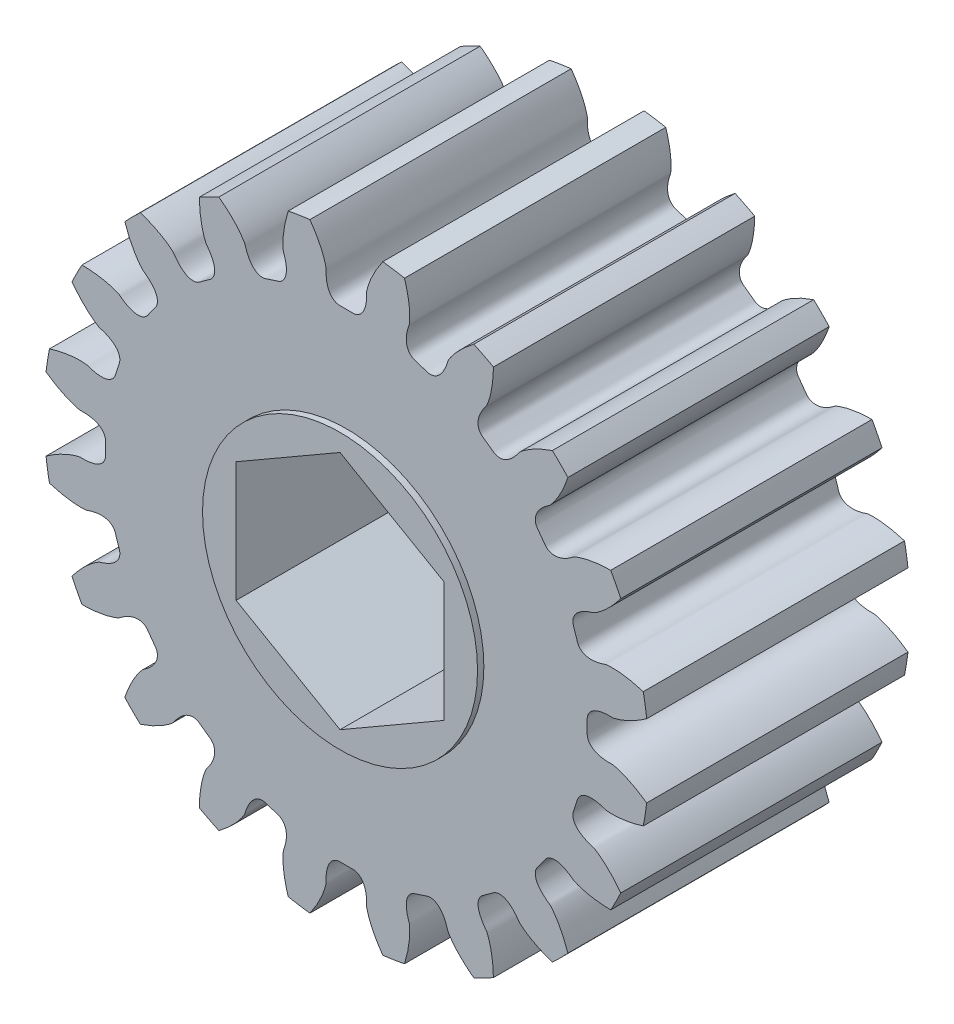
SolidWorks part; units mm, degrees
material "7075-T6 (SN)"
ref_plane "Front Plane" through (0, 0, 0) normal (0, 0, 1) x (1, 0, 0)
ref_plane "Top Plane" through (0, 0, 0) normal (0, 1, 0) x (1, 0, 0)
ref_plane "Right Plane" through (0, 0, 0) normal (1, 0, 0) x (0, 0, -1)
ref_plane "Plane1" through (0, 0, 6.0325) normal (0, 0, 1) x (1, 0, 0)
sketch "Sketch1" plane through (0, 0, 6.0325) normal (0, 0, 1) x (1, 0, 0)
  arc A0 (10.2308, 9.5127) -> (9.5127, 10.2308) centre (0, 0) ccw
  arc A1 (6.7905, 12.2086) -> (5.8856, 12.6697) centre (0, 0) ccw
  arc A2 (2.6855, 13.7094) -> (1.6824, 13.8683) centre (0, 0) ccw
  arc A3 (-1.6824, 13.8683) -> (-2.6855, 13.7094) centre (0, 0) ccw
  arc A4 (-5.8856, 12.6697) -> (-6.7905, 12.2086) centre (0, 0) ccw
  arc A5 (-9.5127, 10.2308) -> (-10.2308, 9.5127) centre (0, 0) ccw
  arc A6 (-12.2086, 6.7905) -> (-12.6697, 5.8856) centre (0, 0) ccw
  arc A7 (-13.7094, 2.6855) -> (-13.8683, 1.6824) centre (0, 0) ccw
  arc A8 (-13.8683, -1.6824) -> (-13.7094, -2.6855) centre (0, 0) ccw
  arc A9 (-12.6697, -5.8856) -> (-12.2086, -6.7905) centre (0, 0) ccw
  arc A10 (-10.2308, -9.5127) -> (-9.5127, -10.2308) centre (0, 0) ccw
  arc A11 (-6.7905, -12.2086) -> (-5.8856, -12.6697) centre (0, 0) ccw
  arc A12 (-2.6855, -13.7094) -> (-1.6824, -13.8683) centre (0, 0) ccw
  arc A13 (1.6824, -13.8683) -> (2.6855, -13.7094) centre (0, 0) ccw
  arc A14 (5.8856, -12.6697) -> (6.7905, -12.2086) centre (0, 0) ccw
  arc A15 (9.5127, -10.2308) -> (10.2308, -9.5127) centre (0, 0) ccw
  arc A16 (12.2086, -6.7905) -> (12.6697, -5.8856) centre (0, 0) ccw
  arc A17 (13.7094, -2.6855) -> (13.8683, -1.6824) centre (0, 0) ccw
  arc A18 (13.8683, 1.6824) -> (13.7094, 2.6855) centre (0, 0) ccw
  arc A19 (12.6697, 5.8856) -> (12.2086, 6.7905) centre (0, 0) ccw
  spline S0 degree 3 number of poles 113 (10.2308, 9.5127) -> (12.2086, 6.7905)
  spline S1 degree 3 number of poles 113 (6.7905, 12.2086) -> (9.5127, 10.2308)
  spline S2 degree 3 number of poles 113 (2.6855, 13.7094) -> (5.8856, 12.6697)
  spline S3 degree 3 number of poles 113 (-1.6824, 13.8683) -> (1.6824, 13.8683)
  spline S4 degree 3 number of poles 113 (-5.8856, 12.6697) -> (-2.6855, 13.7094)
  spline S5 degree 3 number of poles 113 (-9.5127, 10.2308) -> (-6.7905, 12.2086)
  spline S6 degree 3 number of poles 113 (-12.2086, 6.7905) -> (-10.2308, 9.5127)
  spline S7 degree 3 number of poles 113 (-13.7094, 2.6855) -> (-12.6697, 5.8856)
  spline S8 degree 3 number of poles 113 (-13.8683, -1.6824) -> (-13.8683, 1.6824)
  spline S9 degree 3 number of poles 113 (-12.6697, -5.8856) -> (-13.7094, -2.6855)
  spline S10 degree 3 number of poles 113 (-10.2308, -9.5127) -> (-12.2086, -6.7905)
  spline S11 degree 3 number of poles 113 (-6.7905, -12.2086) -> (-9.5127, -10.2308)
  spline S12 degree 3 number of poles 113 (-2.6855, -13.7094) -> (-5.8856, -12.6697)
  spline S13 degree 3 number of poles 113 (1.6824, -13.8683) -> (-1.6824, -13.8683)
  spline S14 degree 3 number of poles 113 (5.8856, -12.6697) -> (2.6855, -13.7094)
  spline S15 degree 3 number of poles 113 (9.5127, -10.2308) -> (6.7905, -12.2086)
  spline S16 degree 3 number of poles 113 (12.2086, -6.7905) -> (10.2308, -9.5127)
  spline S17 degree 3 number of poles 113 (13.7094, -2.6855) -> (12.6697, -5.8856)
  spline S18 degree 3 number of poles 113 (13.8683, 1.6824) -> (13.8683, -1.6824)
  spline S19 degree 3 number of poles 113 (12.6697, 5.8856) -> (13.7094, 2.6855)
extrude "Boss-Extrude1" add sketch "Sketch1" against normal blind 12.065
sketch "Sketch2" plane through (0, 0, 6.0325) normal (0, 0, 1) x (1, 0, 0)
  circle A0 centre (0, 0) radius 6.35
extrude "Boss-Extrude2" add sketch "Sketch2" along normal blind 0.2921
sketch "Sketch3" plane through (0, 0, -6.0325) normal (0, 0, -1) x (-1, 0, 0)
  circle A0 centre (0, 0) radius 6.35
extrude "Boss-Extrude3" add sketch "Sketch3" along normal blind 0.2921
sketch "Sketch4" plane through (0, 0, -6.3246) normal (0, 0, -1) x (-1, 0, 0)
  line L0 (4.8006, 2.7716) -> (0, 5.5433)
  line L1 (0, 5.5433) -> (-4.8006, 2.7716)
  line L2 (-4.8006, 2.7716) -> (-4.8006, -2.7716)
  line L3 (-4.8006, -2.7716) -> (0, -5.5433)
  line L4 (0, -5.5433) -> (4.8006, -2.7716)
  line L5 (4.8006, -2.7716) -> (4.8006, 2.7716)
extrude "Cut-Extrude1" cut sketch "Sketch4" against normal through all
